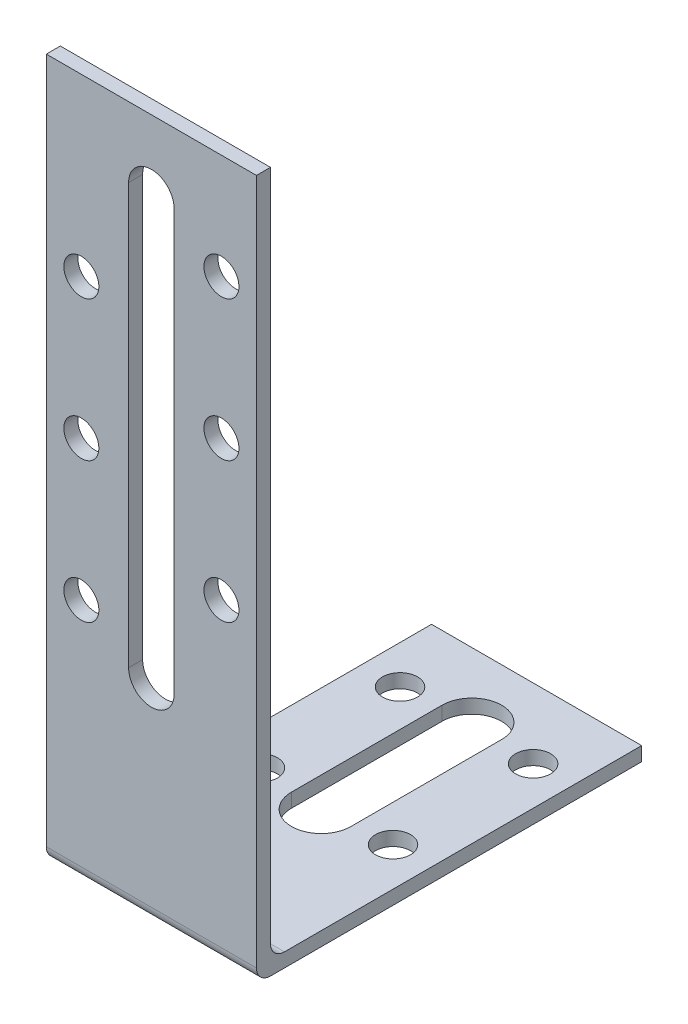
SolidWorks part; units mm, degrees
material "AISI 1020"
ref_plane "Plan de face" through (0, 0, 0) normal (0, 0, 1) x (1, 0, 0)
ref_plane "Plan de dessus" through (0, 0, 0) normal (0, 1, 0) x (1, 0, 0)
ref_plane "Plan de droite" through (0, 0, 0) normal (1, 0, 0) x (0, 0, -1)
sketch "Esquisse1" plane through (0, 0, 0) normal (1, 0, 0) x (0, 0, -1)
  line L0 (0, 0) -> (0, 100)
  line L1 (0, 100) -> (2, 100)
  line L2 (2, 100) -> (2, 2)
  line L3 (2, 2) -> (55, 2)
  line L4 (55, 2) -> (55, 0)
  line L5 (55, 0) -> (0, 0)
  dimension "D1" = 2
  dimension "D2" = 2
  dimension "D3" = 100
  dimension "D4" = 55
extrude "Boss.-Extru.1" add sketch "Esquisse1" along normal mid plane 30
fillet "Congé1" radius 2 2 edges at (0, 0, 0) (0, 2, -2)
sketch "Esquisse2" plane through (0, 2, 0) normal (0, 1, 0) x (1, 0, 0)
  line L0 (0, 24.25) -> (0, 45.75) construction
  line L1 (-4.25, 24.25) -> (-4.25, 45.75)
  line L2 (4.25, 24.25) -> (4.25, 45.75)
  line L4 (15, 55) -> (-15, 55) construction
  line L5 (15, 55) -> (15, 4) construction
  line L6 (-15, 35) -> (15, 35) construction
  line L8 (-15, 55) -> (-15, 4) construction
  line L9 (0, 55) -> (0, 2) construction
  line L10 (15, 2) -> (-15, 2) construction
  arc A0 (-4.25, 24.25) -> (4.25, 24.25) centre (0, 24.25) ccw
  arc A1 (4.25, 45.75) -> (-4.25, 45.75) centre (0, 45.75) ccw
  circle A2 centre (9.5, 45) radius 2.5
  circle A3 centre (9.5, 25) radius 2.5
  circle A4 centre (9.5, 45) radius 2.5
  circle A5 centre (9.5, 25) radius 2.5
  circle A6 centre (-9.5, 45) radius 2.5
  circle A7 centre (-9.5, 25) radius 2.5
  point P3 (0, 35)
  dimension "D1" = 4.25
  dimension "D6" = 5
  dimension "D2" = 21.5
  dimension "D3" = 9.25
  dimension "D4" = 10
  dimension "D5" = 5.5
extrude "Enlèv. mat.-Extru.1" cut sketch "Esquisse2" against normal up to next contours L2 A1 L1 A0 | A7 | A6 | A2 | A3
sketch "Esquisse4" plane through (0, 0, -2) normal (0, 0, -1) x (-1, 0, 0)
  line L0 (0, 90) -> (0, 30) construction
  line L1 (3.25, 90) -> (3.25, 30)
  line L2 (-3.25, 90) -> (-3.25, 30)
  line L3 (-15, 100) -> (15, 100) construction
  line L5 (15, 4) -> (15, 100) construction
  arc A0 (3.25, 90) -> (-3.25, 90) centre (0, 90) ccw
  arc A1 (-3.25, 30) -> (3.25, 30) centre (0, 30) ccw
  circle A2 centre (-10, 85) radius 2.5
  circle A3 centre (-10, 65) radius 2.5
  circle A4 centre (-10, 45) radius 2.5
  circle A5 centre (10, 75) radius 2.5
  circle A6 centre (10, 55) radius 2.5
  circle A7 centre (10, 35) radius 2.5
  point P3 (0, 60)
  dimension "D1" = 3.25
  dimension "D5" = 5
  dimension "D9" = 5
  dimension "D11" = 25
  dimension "D13" = 20
  dimension "D2" = 60
  dimension "D3" = 10
  dimension "D4" = 10
  dimension "D6" = 15
  dimension "D8" = 20
  dimension "D10" = 5
  dimension "D7" = 3
  dimension "D12" = 3
extrude "Enlèv. mat.-Extru.2" cut sketch "Esquisse4" against normal up to next
